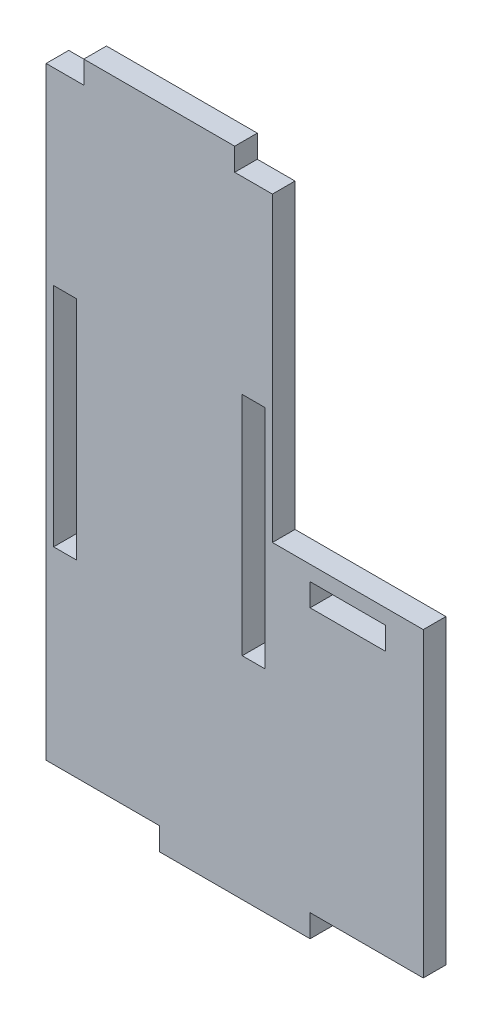
SolidWorks part; units mm, degrees
ref_plane "Front Plane" through (0, 0, 0) normal (0, 0, 1) x (1, 0, 0)
ref_plane "Top Plane" through (0, 0, 0) normal (0, 1, 0) x (1, 0, 0)
ref_plane "Right Plane" through (0, 0, 0) normal (1, 0, 0) x (0, 0, -1)
sketch "Sketch1" plane through (0, 0, 0) normal (0, 0, 1) x (1, 0, 0)
  line L0 (10, 40) -> (15, 40)
  line L1 (-15, 40) -> (-10, 40)
  line L2 (-15, 40) -> (-15, -40)
  line L3 (-15, -40) -> (0, -40)
  line L4 (15, 40) -> (15, 0)
  line L5 (-15, 40) -> (15, -40) construction
  line L6 (-15, -40) -> (15, 40) construction
  line L7 (-14, 15) -> (-11, 15)
  line L8 (-14, 15) -> (-14, -15)
  line L9 (-14, -15) -> (-11, -15)
  line L10 (-11, 15) -> (-11, -15)
  line L11 (11, 15) -> (14, 15)
  line L12 (11, 15) -> (11, -15)
  line L13 (11, -15) -> (14, -15)
  line L14 (14, 15) -> (14, -15)
  line L15 (15, 0) -> (35, 0)
  line L17 (20, -40) -> (35, -40)
  line L18 (35, 0) -> (35, -40)
  line L20 (0, -40) -> (0, -43)
  line L21 (0, -43) -> (20, -43)
  line L22 (20, -40) -> (20, -43)
  line L24 (-10, 40) -> (-10, 43)
  line L25 (-10, 43) -> (10, 43)
  line L26 (10, 40) -> (10, 43)
  line L27 (20, -2) -> (30, -2)
  line L28 (20, -2) -> (20, -5)
  line L29 (20, -5) -> (30, -5)
  line L30 (30, -2) -> (30, -5)
  point P0 (0, 0)
  point P1 (0, 0)
  dimension "D1" = 30
  dimension "D2" = 80
  dimension "D3" = 3
  dimension "D4" = 3
  dimension "D5" = 1
  dimension "D6" = 30
  dimension "D7" = 25
  dimension "D8" = 25
  dimension "D9" = 30
  dimension "D10" = 1
  dimension "D11" = 20
  dimension "D12" = 3
  dimension "D13" = 15
  dimension "D14" = 20
  dimension "D15" = 5
  dimension "D16" = 10
  dimension "D17" = 35
  dimension "D18" = 3
  dimension "D19" = 5
  dimension "D20" = 20
  dimension "D21" = 3
extrude "Boss-Extrude2" add sketch "Sketch1" along normal mid plane 3
